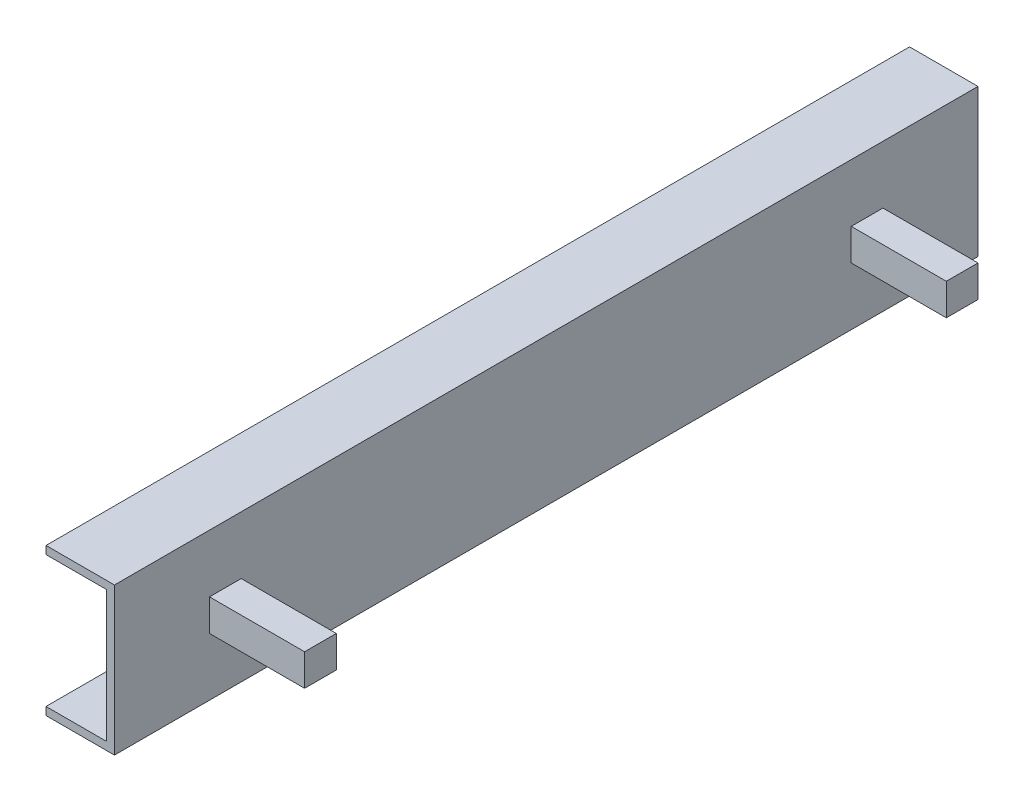
SolidWorks part; units mm, degrees
ref_plane "Front Plane" through (0, 0, 0) normal (0, 0, 1) x (1, 0, 0)
ref_plane "Top Plane" through (0, 0, 0) normal (0, 1, 0) x (1, 0, 0)
ref_plane "Right Plane" through (0, 0, 0) normal (1, 0, 0) x (0, 0, -1)
sketch "Sketch1" plane through (0, 0, 0) normal (0, 0, 1) x (1, 0, 0)
  line L0 (0, 0) -> (0, 59.055)
  line L1 (0, 59.055) -> (-54.864, 59.055)
  line L2 (-54.864, 59.055) -> (-54.864, 52.705)
  line L3 (-54.864, 52.705) -> (-6.35, 52.705)
  line L4 (-6.35, 52.705) -> (-6.35, 0)
  line L5 (-6.35, 0) -> (0, 0)
  dimension "D1" = 6.35
  dimension "D2" = 59.055
  dimension "D3" = 54.864
extrude "Boss-Extrude1" add sketch "Sketch1" along normal mid plane 692.15
mirror "Mirror1" about plane through (-6.35, 0, 346.075) normal (0, 1, 0) of "Boss-Extrude1"
sketch "Sketch2" plane through (0, 0, 0) normal (1, 0, 0) x (0, 0, -1)
  line L0 (-346.075, -59.055) -> (-346.075, 59.055) construction
  line L1 (-269.875, -12.7) -> (-244.475, -12.7)
  line L2 (-269.875, -12.7) -> (-269.875, 12.7)
  line L3 (-269.875, 12.7) -> (-244.475, 12.7)
  line L4 (-244.475, -12.7) -> (-244.475, 12.7)
  line L5 (-269.875, -12.7) -> (-244.475, 12.7) construction
  line L6 (-269.875, 12.7) -> (-244.475, -12.7) construction
  line L7 (-257.175, 59.055) -> (-257.175, 0) construction
  line L8 (-346.075, 59.055) -> (346.075, 59.055) construction
  line L9 (-257.175, 0) -> (-257.175, -59.055) construction
  line L10 (-346.075, -59.055) -> (346.075, -59.055) construction
  point P0 (-257.175, 0)
  dimension "D1" = 25.4
  dimension "D2" = 76.2
extrude "Boss-Extrude2" add sketch "Sketch2" along normal blind 76.2
mirror "Mirror2" about plane through (0, 0, 0) normal (0, 0, 1) of "Boss-Extrude2"
ref_plane "Plane1" through (76.2, 0, 0) normal (1, 0, 0) x (0, 0, -1)
